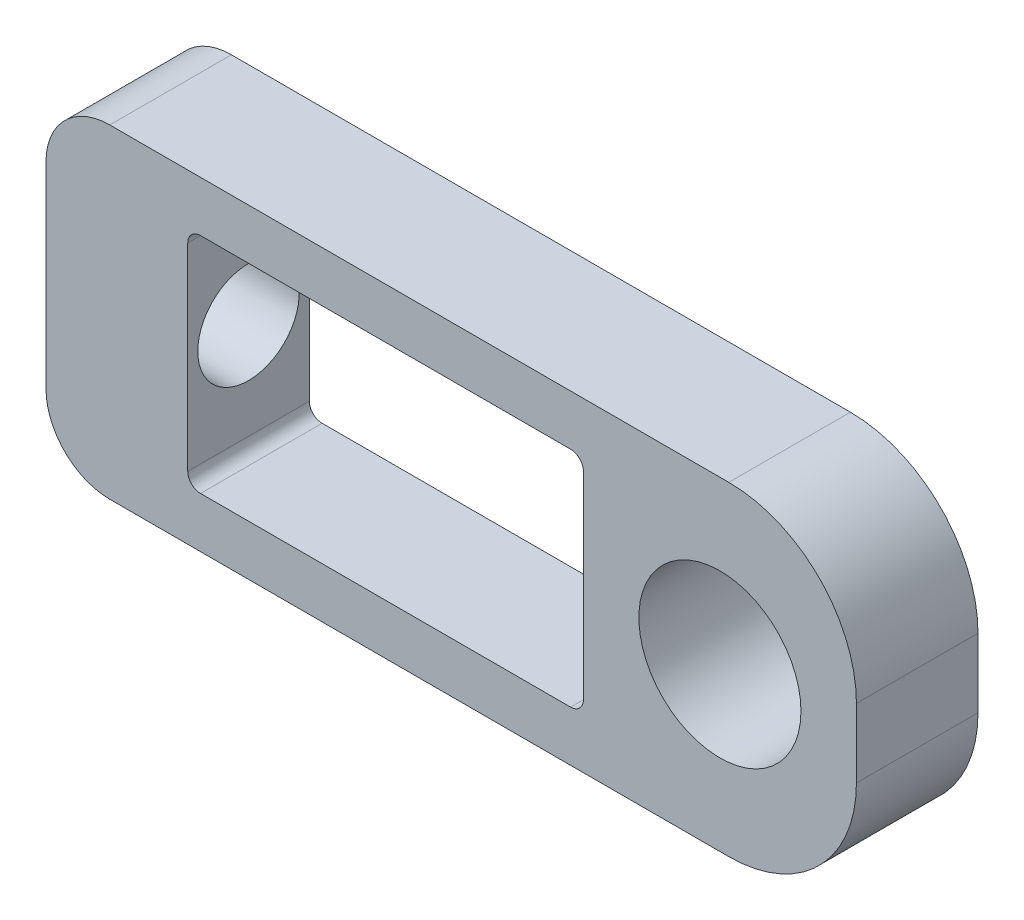
SolidWorks part; units mm, degrees
ref_plane "Front Plane" through (0, 0, 0) normal (0, 0, 1) x (1, 0, 0)
ref_plane "Top Plane" through (0, 0, 0) normal (0, 1, 0) x (1, 0, 0)
ref_plane "Right Plane" through (0, 0, 0) normal (1, 0, 0) x (0, 0, -1)
sketch "Sketch1" plane through (0, 0, 0) normal (0, 0, 1) x (1, 0, 0)
  line L1 (0, 0) -> (63.5, 0)
  line L2 (0, 0) -> (0, 25.4)
  line L3 (0, 25.4) -> (63.5, 25.4)
  line L4 (63.5, 0) -> (63.5, 25.4)
  dimension "D1" = 63.5
  dimension "D2" = 25.4
extrude "Boss-Extrude1" add sketch "Sketch1" along normal blind 9.525
sketch "Sketch5" plane through (0, 0, 9.525) normal (0, 0, 1) x (1, 0, 0)
  line L0 (42.1062, 12.7) -> (63.5, 12.7) construction
  line L1 (63.5, 0) -> (63.5, 25.4) construction
  line L6 (11.1062, 3.95) -> (42.1062, 3.95)
  line L7 (11.1062, 3.95) -> (11.1062, 21.45)
  line L8 (11.1062, 21.45) -> (42.1062, 21.45)
  line L9 (42.1062, 3.95) -> (42.1062, 21.45)
  line L10 (11.1062, 3.95) -> (42.1062, 21.45) construction
  line L11 (11.1062, 21.45) -> (42.1062, 3.95) construction
  circle A1 centre (52.8031, 12.7) radius 6.35
  point P11 (26.6062, 12.7)
  dimension "D1" = 12.7
  dimension "D2" = 31
  dimension "D3" = 17.5
extrude "Cut-Extrude3" cut sketch "Sketch5" against normal through all
sketch "Sketch4" plane through (0, 0, 0) normal (-1, 0, 0) x (0, 0, 1)
  line L0 (0, 25.4) -> (9.525, 0) construction
  circle A1 centre (4.7625, 12.7) radius 3.9751
  dimension "D1" = 7.9502
extrude "Cut-Extrude2" cut sketch "Sketch4" against normal up to next
fillet "Fillet4" radius 10 2 edges at (63.5, 0, 4.7625) (63.5, 25.4, 4.7625)
fillet "Fillet5" radius 5 2 edges at (0, 0, 4.7625) (0, 25.4, 4.7625)
fillet "Fillet6" radius 1 4 edges at (11.1062, 21.45, 4.7625) (11.1062, 3.95, 4.7625) (42.1062, 3.95, 4.7625) (42.1062, 21.45, 4.7625)
ref_plane "Plane1" through (0, 0, 4.7625) normal (0, 0, 1) x (1, 0, 0)
